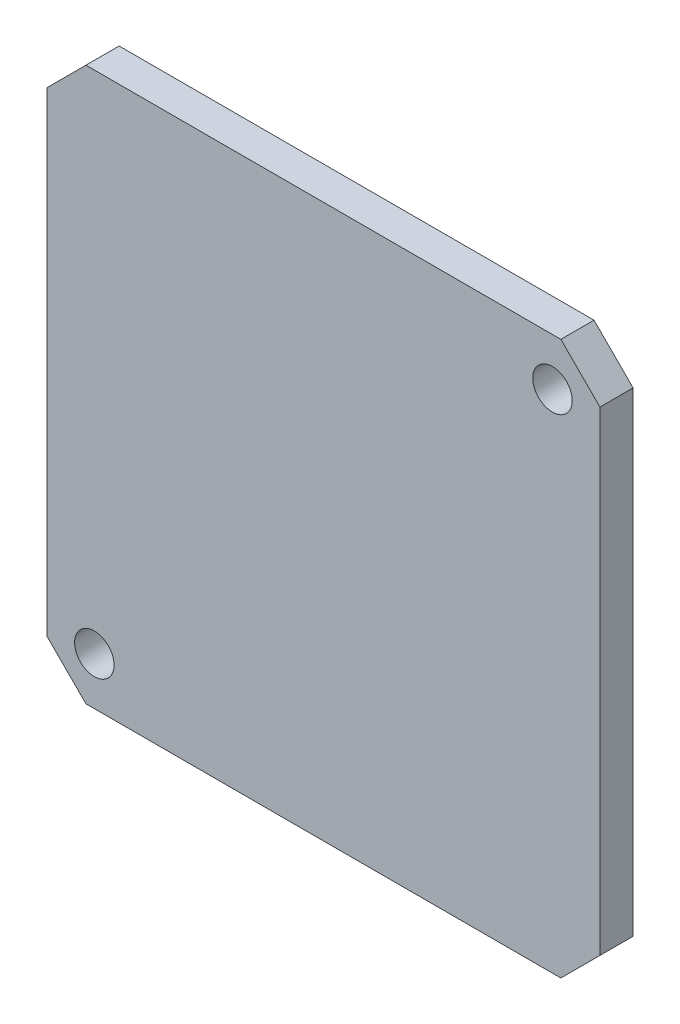
SolidWorks part; units mm, degrees
ref_plane "Front Plane" through (0, 0, 0) normal (0, 0, 1) x (1, 0, 0)
ref_plane "Top Plane" through (0, 0, 0) normal (0, 1, 0) x (1, 0, 0)
ref_plane "Right Plane" through (0, 0, 0) normal (1, 0, 0) x (0, 0, -1)
sketch "Sketch1" plane through (0, 0, 0) normal (0, 0, 1) x (1, 0, 0)
  line L0 (-17.5, 15.0269) -> (-17.5, -15.0269)
  line L1 (-17.5, -15.0269) -> (-15.0269, -17.5)
  line L2 (-15.0269, -17.5) -> (15.0269, -17.5)
  line L3 (15.0269, -17.5) -> (17.5, -15.0269)
  line L4 (17.5, -15.0269) -> (17.5, 15.0269)
  line L5 (17.5, 15.0269) -> (15.0269, 17.5)
  line L6 (15.0269, 17.5) -> (-15.0269, 17.5)
  line L7 (-15.0269, 17.5) -> (-17.5, 15.0269)
  circle A0 centre (14.4957, 14.4957) radius 1.25
  circle A1 centre (-14.4957, -14.4957) radius 1.25
extrude "Boss-Extrude1" add sketch "Sketch1" along normal blind 2.1
